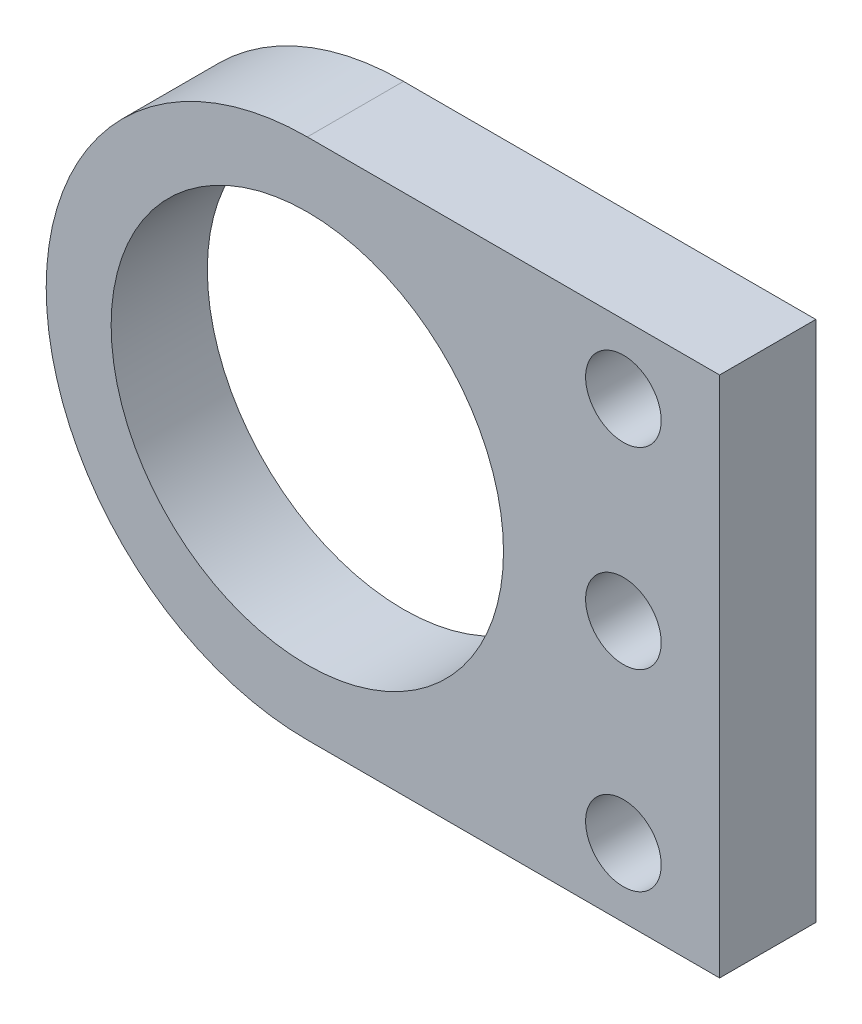
SolidWorks part; units mm, degrees
ref_plane "Front Plane" through (0, 0, 0) normal (0, 0, 1) x (1, 0, 0)
ref_plane "Top Plane" through (0, 0, 0) normal (0, 1, 0) x (1, 0, 0)
ref_plane "Right Plane" through (0, 0, 0) normal (1, 0, 0) x (0, 0, -1)
sketch "Sketch1" plane through (0, 0, 0) normal (0, 0, 1) x (1, 0, 0)
  line L0 (0, -19) -> (30, -19)
  line L1 (30, -19) -> (30, 19)
  line L2 (30, 19) -> (0, 19)
  circle A0 centre (0, 0) radius 14.275
  arc A1 (0, -19) -> (0, 19) centre (0, 0) cw
  circle A2 centre (23, 14) radius 2.75
  circle A3 centre (23, 0) radius 2.75
  circle A4 centre (23, -14) radius 2.75
  point P13 (0, 0)
  point P14 (0, 0)
  point P15 (0, 0)
  dimension "D1" = 28.55
  dimension "D2" = 19
  dimension "D3" = 5.5
  dimension "D4" = 5.5
  dimension "D5" = 5.5
  dimension "D6" = 5
  dimension "D7" = 5
  dimension "D8" = 7
  dimension "D9" = 30
extrude "Boss-Extrude1" add sketch "Sketch1" along normal blind 7
